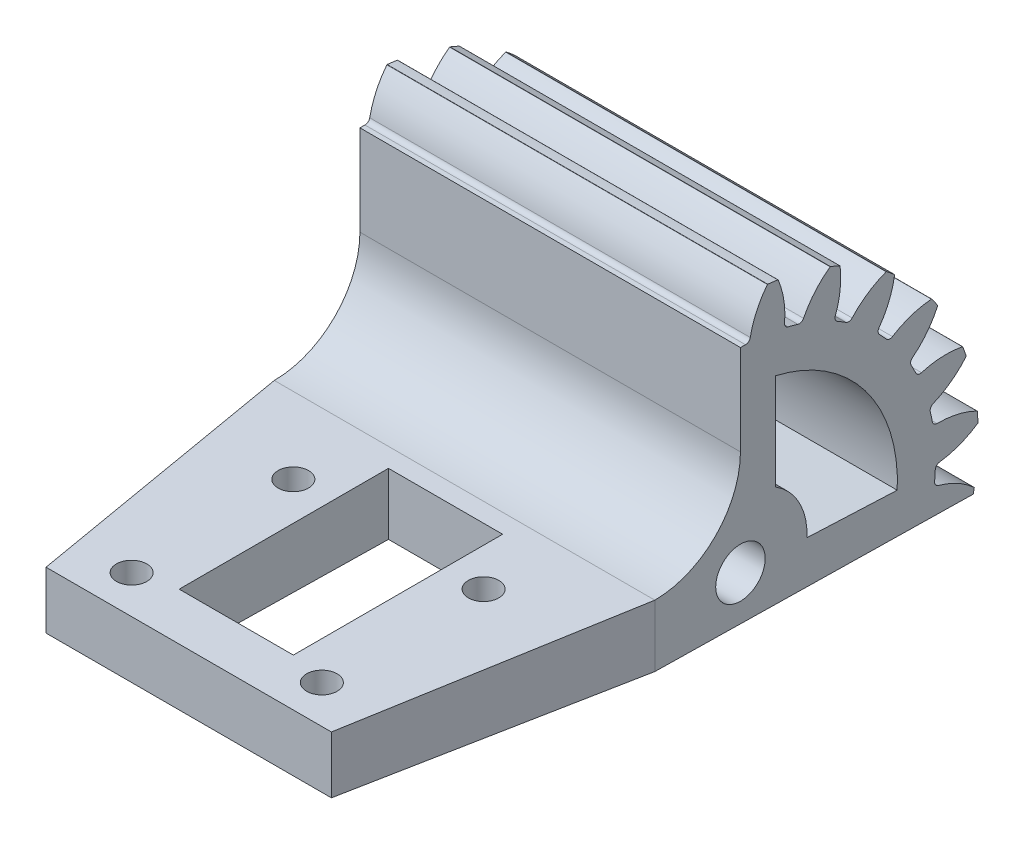
SolidWorks part; units mm, degrees
ref_plane "Plane1" through (0, 0, 0) normal (0, 0, 1) x (1, 0, 0)
ref_plane "Plane2" through (0, 0, 0) normal (0, 1, 0) x (1, 0, 0)
ref_plane "Plane3" through (0, 0, 0) normal (1, 0, 0) x (0, 0, -1)
other "Configuration Table"
sketch "HoldingSke" plane through (0, 0, 0) normal (0, 1, 0) x (1, 0, 0)
  line L0 (0, 0) -> (0.4603, -0.1954)
  line L1 (-15, 0) -> (100, 0) construction
  line L2 (0, 0) -> (-2.1039, 2.3779)
  line L3 (0, 0) -> (-11.863, 4.5341)
  line L4 (0, 0) -> (7.9495, 3.3744)
  line L5 (0, 0) -> (-46.8476, -17.4728)
  line L6 (0, 0) -> (-33.1585, -22.3721)
  line L7 (-2.1039, 2.3779) -> (8.6586, 51.2059)
  line L8 (-76.2, 54.61) -> (-76.1, 54.61)
  line L9 (-71.009, 38.7566) -> (-53.1078, 45.2721)
  line L10 (-76.2, 71.12) -> (104.1128, 71.12)
  line L11 (0, 0) -> (-40, 0)
  line L12 (-76.2, 101.6) -> (-76.133, 101.6)
  line L13 (24.9733, 27.94) -> (52.9518, 28.4284)
  line L14 (24.9733, 27.94) -> (24.9743, 27.94)
  line L15 (24.9733, 27.94) -> (100.4006, 29.5858)
  line L16 (-63.627, -2) -> (-12.827, -2)
  circle A0 centre (0, 0) radius 0.4
  circle A1 centre (0, 0) radius 20.499
  circle A2 centre (0, 0) radius 37.5
  circle A3 centre (0, 0) radius 0.4
  dimension "MHD" = 40.998
  dimension "Hub_dia" = 75
  dimension "Bore" = 0.8
  dimension "MBD" = 0.8
  dimension "Num_teeth" = 23
  dimension "Pitch" = 0.5
  dimension "Overall_len" = 50
  dimension "Show_teeth" = 23
  dimension "Thickness" = 40
  dimension "OAL" = 50.0001
  dimension "T_dim" = 0.1
  dimension "Ap" = 20
  dimension "H" = 19.05
  dimension "Pitch_radius" = 180.3128
  dimension "Width" = 40
  dimension "Backlash" = 0.067
  dimension "Addendum_fac" = 1
  dimension "Dedendum_fac" = 1.25
  dimension "Clearance_fac" = 0.25
  dimension "Dedendum_add" = 0.001
  dimension "Module" = 2
sketch "BasProSke" plane through (0, 0, 0) normal (0, 1, 0) x (1, 0, 0)
  line L0 (-10, 0) -> (60, 0) construction
  line L1 (0, 0) -> (0, 25)
  line L2 (0, 0) -> (40, 0)
  line L3 (40, 0) -> (40, 25)
  line L4 (40, 25) -> (0, 25)
  dimension "Thickness" = 40
  dimension "Diameter" = 50
revolve "Base-Revolve" add sketch "BasProSke" angle 360 about L0
sketch "TooCutSke" plane through (0, 0, 0) normal (1, 0, 0) x (0, 0, -1)
  line L1 (0, 0) -> (0, 107) construction
  line L2 (0, 0) -> (-1.6868, 22.9381) construction
  line L3 (0, 0) -> (-6.2512, 45.4806) construction
  line L4 (-1.6868, 22.9381) -> (-3.1256, 22.7403) construction
  arc A0 (0.9602, 20.4765) -> (-0.9602, 20.4765) centre (0, 0) ccw
  arc A1 (2.8652, 24.8608) -> (-2.8652, 24.8608) centre (0, 0) ccw
  circle A2 centre (0, 0) radius 23 construction
  circle A3 centre (0, 0) radius 21.6129 construction
  arc A4 (-0.9602, 20.4765) -> (-2.8652, 24.8608) centre (-10.0609, 19.1284) ccw
  arc A5 (2.8652, 24.8608) -> (0.9602, 20.4765) centre (10.0609, 19.1284) ccw
  dimension "Root_dia" = 40.998
  dimension "Overcut_dia" = 50.0508
  dimension "Pitch_dia" = 46
  dimension "Base_dia" = 43.2259
  dimension "Flank_rad" = 9.2
  dimension "Half_ang" = 7.826
  dimension "Half_CT" = 1.4523
extrude "ToothCut" cut sketch "TooCutSke" along normal through all
fillet "Breaks" radius 0.04 2 edges at (20, 24.8374, -2.8466) (20, 24.8374, 2.8466)
fillet "RootFillets" radius 0.501 2 edges at (20, 20.4765, -0.9602) (20, 20.4765, 0.9602)
pattern_circular "TeethCuts" count 23 every 15.652 about axis through (-10, 0, 0) along (1, 0, 0) of "ToothCut", "RootFillets", "Breaks"
sketch "HubNeaOneSke" plane through (0, 0, 0) normal (-1, 0, 0) x (0, 0, 1)
  circle A0 centre (0, 0) radius 20.499
  dimension "Diameter" = 40.998
extrude "HubNearOne" [suppressed] add sketch "HubNeaOneSke" along normal blind 10.0001
sketch "HubNeaBotSke" plane through (0, 0, 0) normal (-1, 0, 0) x (0, 0, 1)
  circle A0 centre (0, 0) radius 20.499
  dimension "Diameter" = 40.998
extrude "HubNearBoth" [suppressed] add sketch "HubNeaBotSke" along normal blind 5
ref_plane "FarPln" through (40, 0, 0) normal (1, 0, 0) x (0, 0, -1)
sketch "HubFarSke" plane through (40, 0, 0) normal (1, 0, 0) x (0, 0, -1)
  circle A0 centre (0, 0) radius 20.499
  dimension "Diameter" = 40.998
extrude "HubFar" [suppressed] add sketch "HubFarSke" along normal blind 5
sketch "BorSke" plane through (0, 0, 0) normal (1, 0, 0) x (0, 0, -1)
  circle A0 centre (0, 0) radius 0.4
  dimension "Diameter" = 0.8
extrude "Bore" cut sketch "BorSke" along normal mid plane 100.0001
sketch "KeySke" plane through (0, 0, 0) normal (1, 0, 0) x (0, 0, -1)
  line L0 (-0.05, 0) -> (-0.05, 0.5)
  line L1 (-0.05, 0.5) -> (0.05, 0.5)
  line L2 (0.05, 0.5) -> (0.05, 0)
  line L3 (0, 0) -> (0, 34) construction
  line L4 (-0.05, 0) -> (0.05, 0)
  dimension "Offset" = 0.5
  dimension "Width" = 0.1
extrude "Keyway" [suppressed] cut sketch "KeySke" along normal mid plane 100.0001
pattern_circular "Keyway2" [suppressed] count 2 every 90 about axis through (-10, 0, 0) along (1, 0, 0)
sketch "草图1" plane through (40, 0, 0) normal (1, 0, 0) x (0, 0, -1)
  line L0 (0, 25.4034) -> (0, 0)
  line L3 (36.2238, -7.5274) -> (19.5237, -38.1691)
  line L4 (19.5237, -38.1691) -> (-51.0927, -13.8803)
  line L5 (-51.0927, -13.8803) -> (-19.9975, 29.428)
  line L6 (-19.9975, 29.428) -> (0, 25.4034)
  line L7 (0, 0) -> (24.4771, -5.0864)
  line L8 (24.4771, -5.0864) -> (36.2238, -7.5274)
  arc A0 (24.3616, -5.6136) -> (24.5812, -4.5568) centre (0, 0) ccw construction
extrude "切除-拉伸1" cut sketch "草图1" against normal through all
sketch "草图3" plane through (0, 0, 0) normal (-1, 0, 0) x (0, 0, 1)
  circle A0 centre (0, 0) radius 1.6
extrude "切除-拉伸2" cut sketch "草图3" against normal through all
sketch "草图4" plane through (0, 0, 0) normal (-1, 0, 0) x (0, 0, 1)
  line L2 (0, 1.6) -> (0, 20.499) construction
  line L5 (0, 11) -> (0, 4)
  line L6 (0, 4) -> (0, 1.6)
  line L8 (15.9995, 2) -> (37.9995, 2)
  line L9 (37.9995, 2) -> (37.9995, -4)
  line L12 (-24.4771, -5.0864) -> (-1.5665, -0.3255)
  line L15 (-24.4771, -5.0864) -> (37.9995, -4)
  line L16 (9, 2) -> (15.9995, 2)
  arc A0 (-1.5665, -0.3255) -> (0, 1.6) centre (0, 0) ccw
  arc A1 (0, 11) -> (9, 2) centre (9, 11) ccw
  dimension "D2" = 22
  dimension "D4" = 9
  dimension "D1" = 2
  dimension "D3" = 6
  dimension "D6" = 9
extrude "凸台-拉伸1" add sketch "草图4" against normal blind 40
sketch "草图5" plane through (0, 2, 0) normal (0, 1, 0) x (1, 0, 0)
  line L0 (20, 24.8971) -> (20, -15.9995) construction
  line L3 (20, -15.9995) -> (20, -37.9995) construction
  line L4 (40, -37.9995) -> (0, -37.9995) construction
  line L5 (40, -9) -> (0, -9) construction
  circle A0 centre (10, -17) radius 1.6
  circle A1 centre (10, -34) radius 1.6
  circle A2 centre (30, -34) radius 1.6
  circle A3 centre (30, -17) radius 1.6
  dimension "D1" = 10
  dimension "D2" = 10
  dimension "D3" = 8
extrude "切除-拉伸3" cut sketch "草图5" against normal through all
sketch "草图7" plane through (0, 0, 0) normal (-1, 0, 0) x (0, 0, 1)
  line L2 (-6.9931, -0.3104) -> (-16.4838, -0.7316)
  line L3 (-24.4771, -5.0864) -> (0, -4) construction
  line L4 (-3.6969, 5.9441) -> (-3.6969, 16.0805)
  arc A0 (-3.6969, 16.0805) -> (-16.4838, -0.7316) centre (0, 0) ccw
  arc A1 (-3.6969, 5.9441) -> (-6.9931, -0.3104) centre (0, 0) ccw
  dimension "D1" = 14
  dimension "D2" = 33
extrude "切除-拉伸5" cut sketch "草图7" against normal through all
sketch "草图8" plane through (0, 2, 0) normal (0, 1, 0) x (1, 0, 0)
  line L0 (20, -37.9995) -> (20, -9) construction
  line L1 (40, -37.9995) -> (0, -37.9995) construction
  line L2 (40, -9) -> (0, -9) construction
  line L3 (26, -32.9995) -> (14, -32.9995)
  line L8 (14, -32.9995) -> (14, -10.9995)
  line L9 (14, -10.9995) -> (26, -10.9995)
  line L10 (26, -32.9995) -> (26, -10.9995)
  point P12 (20, -23.4998)
  dimension "D1" = 22
  dimension "D2" = 5
  dimension "D3" = 6
  dimension "D4" = 6
extrude "切除-拉伸6" cut sketch "草图8" against normal through all
sketch "草图10" plane through (0, 0, 0) normal (-1, 0, 0) x (0, 0, 1)
  circle A0 centre (0, 0) radius 2.6
extrude "切除-拉伸7" cut sketch "草图10" against normal through all
sketch "草图11" plane through (0, 2, 0) normal (0, 1, 0) x (1, 0, 0)
  line L0 (35, -37.9995) -> (40, -9)
  line L1 (40, -37.9995) -> (0, -37.9995) construction
  line L2 (35, -94) -> (35, -12) construction
  line L3 (40, -9) -> (40, -37.9995)
  line L4 (40, -37.9995) -> (35, -37.9995)
  line L5 (0, -37.9995) -> (5, -37.9995)
  line L6 (5, -12) -> (5, -94) construction
  line L7 (5, -37.9995) -> (0, -9)
  line L8 (0, -37.9995) -> (0, -9) construction
  line L9 (0, -9) -> (0, -37.9995)
extrude "切除-拉伸8" cut sketch "草图11" against normal through all
equation "' \"Module@HoldingSke\" = 6.35"
equation "' \"Num_teeth@HoldingSke\" = 12"
equation "' \"Ap@HoldingSke\" =  20"
equation "' \"Ap@HoldingSke\" = 20"
equation "' \"Width@HoldingSke\" = 0.5 * 25.4"
equation "' \"Hub_dia@HoldingSke\"= 1 * 25.4"
equation "' \"Hub_dia@HoldingSke\" = 1 * 25.4"
equation "' \"Overall_len@HoldingSke\" = 1.0 * 25.4"
equation "' \"Bore@HoldingSke\" = 0.75 * 25.4"
equation "' \"T_dim@HoldingSke\" = 0.1 * 25.4"
equation "' \"Width@KeySke\" = 0.25 * 25.4"
equation "' \"Show_teeth@HoldingSke\" = 13"
equation "' \"Backlash@HoldingSke\" = 0.009 * 25.4"
equation "' \"Addendum_fac@HoldingSke\" = 1.0"
equation "' \"Dedendum_fac@HoldingSke\" = 1.25"
equation "' \"Dedendum_add@HoldingSke\" = 0.00005 * 25.4"
equation "' \"Clearance_fac@HoldingSke\" = 0.25"
equation "\"Pitch@HoldingSke\" = 1 / \"Module@HoldingSke\""
equation "\"Overcut_dia@TooCutSke\" = (\"Num_teeth@HoldingSke\" + 2 * \"Addendum_fac@HoldingSke\") / \"Pitch@HoldingSke\" + 0.002 * 25.4"
equation "\"Pitch_dia@TooCutSke\" = \"Num_teeth@HoldingSke\" / \"Pitch@HoldingSke\""
equation "\"Base_dia@TooCutSke\" = \"Num_teeth@HoldingSke\" / \"Pitch@HoldingSke\" * cos((\"Ap@HoldingSke\"  * 3.14159265 / 180))"
equation "\"Root_dia@TooCutSke\" = (\"Num_teeth@HoldingSke\" + 2) / \"Pitch@HoldingSke\" - 2 * (\"Addendum_fac@HoldingSke\" + \"Dedendum_fac@HoldingSke\") / \"Pitch@HoldingSke\" - \"Dedendum_add@HoldingSke\" * 2"
equation "\"Half_ang@TooCutSke\" = 180 / \"Num_teeth@HoldingSke\""
equation "\"Half_CT@TooCutSke\" = \"Num_teeth@HoldingSke\" / \"Pitch@HoldingSke\" * sin((3.14159265 / 2 / \"Num_teeth@HoldingSke\")) / 2 - 7 * \"Backlash@HoldingSke\" / 4"
equation "\"Flank_rad@TooCutSke\" = \"Num_teeth@HoldingSke\" / \"Pitch@HoldingSke\" / 5"
equation "\"Radius@RootFillets\" = \"Clearance_fac@HoldingSke\" / \"Pitch@HoldingSke\" + \"Dedendum_add@HoldingSke\""
equation "\"Break_rad@Breaks\" = 0.02 / \"Pitch@HoldingSke\""
equation "\"Thickness@HoldingSke\" = \"Width@HoldingSke\""
equation "\"OAL@HoldingSke\" = \"Thickness@HoldingSke\""
equation "\"MHD@HoldingSke\" = (\"Num_teeth@HoldingSke\" + 2) / \"Pitch@HoldingSke\" - 2 * (\"Addendum_fac@HoldingSke\" + \"Dedendum_fac@HoldingSke\")  / \"Pitch@HoldingSke\" - \"Dedendum_add@HoldingSke\" * 2"
equation "\"MBD@HoldingSke\" = (\"Num_teeth@HoldingSke\" + 2) / \"Pitch@HoldingSke\" - 2 * (\"Addendum_fac@HoldingSke\" + \"Dedendum_fac@HoldingSke\")  / \"Pitch@HoldingSke\" - \"Dedendum_add@HoldingSke\" * 2 - 0.002 * 25.4"
equation "\"MHD@HoldingSke\" = ((sgn( \"MHD@HoldingSke\" - \"Hub_dia@HoldingSke\" )-1)*( \"MHD@HoldingSke\" - \"Hub_dia@HoldingSke\" ))/-2+ \"Hub_dia@HoldingSke\""
equation "\"MBD@HoldingSke\" = ((sgn( \"MBD@HoldingSke\" - \"Bore@HoldingSke\" )-1)*( \"MBD@HoldingSke\" - \"Bore@HoldingSke\" ))/-2+ \"Bore@HoldingSke\""
equation "\"OAL@HoldingSke\" = ((sgn( \"OAL@HoldingSke\" - \"Overall_len@HoldingSke\" )+1)*( \"OAL@HoldingSke\" - \"Overall_len@HoldingSke\" ))/2 + \"Overall_len@HoldingSke\" + 0.000002 * 25.4"
equation "\"Num_teeth@TeethCuts\" = int( \"Show_teeth@HoldingSke\" ) + 1"
equation "\"Num_teeth@TeethCuts\" = ((sgn( \"Num_teeth@TeethCuts\" - \"Num_teeth@HoldingSke\" )-1)*( \"Num_teeth@TeethCuts\" - \"Num_teeth@HoldingSke\" ))/-2+ \"Num_teeth@HoldingSke\""
equation "\"Num_teeth@TeethCuts\" = ((sgn( \"Num_teeth@TeethCuts\" - 2.0)+1)*( \"Num_teeth@TeethCuts\" - 2.0))/2 +2.0"
equation "\"Angle@TeethCuts\" = 360.0 / \"Num_teeth@HoldingSke\""
equation "\"Diameter@BasProSke\" = (\"Num_teeth@HoldingSke\" + 2 * \"Addendum_fac@HoldingSke\") / \"Pitch@HoldingSke\""
equation "\"Thickness@BasProSke\"  = \"Thickness@HoldingSke\""
equation "' \"Fillet_rad@BasProSke\" =  \"Thickness@HoldingSke\" * 0.05"
equation "' \"Fillet_rad@BasProSke\" = \"Thickness@HoldingSke\" * 0.05"
equation "\"MHD@HoldingSke\" = ((sgn( \"MHD@HoldingSke\" - \"Root_dia@TooCutSke\" )-1)*( \"MHD@HoldingSke\" - \"Root_dia@TooCutSke\" ))/-2+ \"Root_dia@TooCutSke\""
equation "\"Diameter@HubNeaOneSke\" = \"MHD@HoldingSke\""
equation "\"Length@HubNearOne\" = \"OAL@HoldingSke\" - \"Thickness@BasProSke\""
equation "\"Diameter@HubNeaBotSke\" = \"MHD@HoldingSke\""
equation "\"Length@HubNearBoth\" = ( \"OAL@HoldingSke\" - \"Thickness@BasProSke\" ) / 2.0"
equation "\"Thickness@FarPln\" = \"Thickness@BasProSke\""
equation "\"Diameter@HubFarSke\" = \"MHD@HoldingSke\""
equation "\"Length@HubFar\" = ( \"OAL@HoldingSke\" - \"Thickness@BasProSke\" ) / 2.0"
equation "\"Diameter@BorSke\" = \"MBD@HoldingSke\""
equation "\"D1@Bore\" = \"OAL@HoldingSke\" * 2.0"
equation "\"D1@Keyway\" = \"OAL@HoldingSke\" * 2.0"
equation "\"Offset@KeySke\" = \"T_dim@HoldingSke\" + \"MBD@HoldingSke\" / 2.0"
